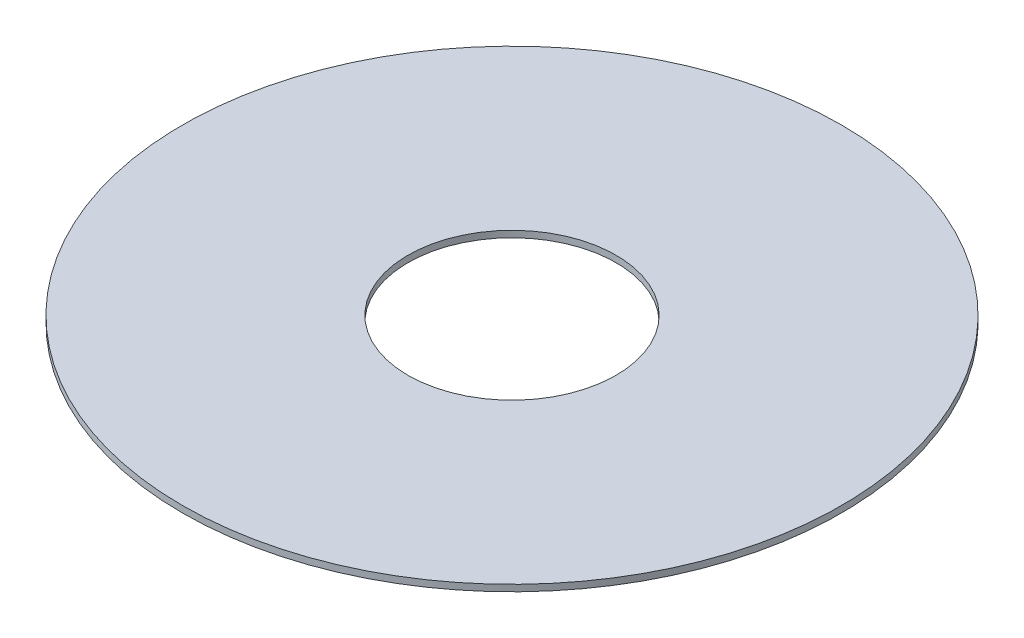
SolidWorks part; units mm, degrees
ref_plane "Front Plane" through (0, 0, 0) normal (0, 0, 1) x (1, 0, 0)
ref_plane "Top Plane" through (0, 0, 0) normal (0, 1, 0) x (1, 0, 0)
ref_plane "Right Plane" through (0, 0, 0) normal (1, 0, 0) x (0, 0, -1)
sketch "Sketch1" plane through (0, 0, 0) normal (0, 1, 0) x (1, 0, 0)
  circle A0 centre (0, 0) radius 241.3
  circle A1 centre (0, 0) radius 76.2
  dimension "D1" = 482.6
  dimension "D2" = 152.4
extrude "Boss-Extrude1" add sketch "Sketch1" along normal blind 4.7625
